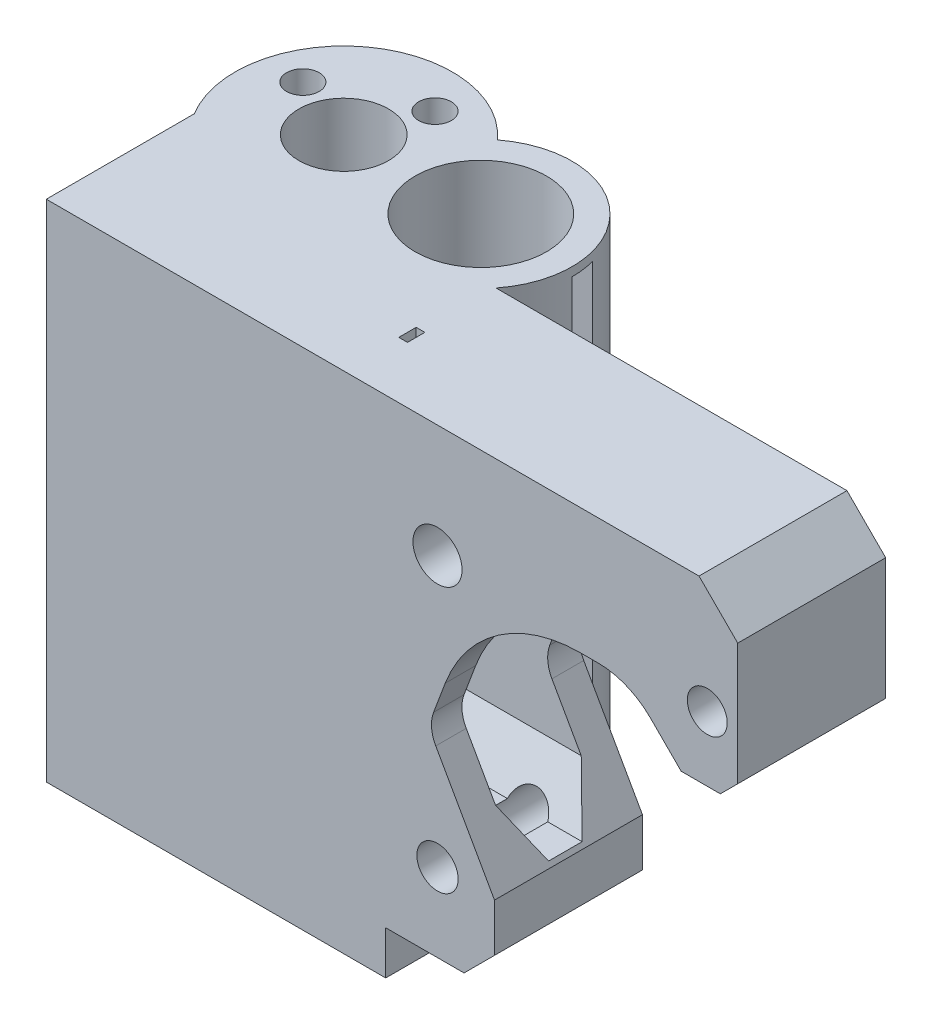
SolidWorks part; units mm, degrees
ref_plane "Front Plane" through (0, 0, 0) normal (0, 0, 1) x (1, 0, 0)
ref_plane "Top Plane" through (0, 0, 0) normal (0, 1, 0) x (1, 0, 0)
ref_plane "Right Plane" through (0, 0, 0) normal (1, 0, 0) x (0, 0, -1)
sketch "Sketch1" plane through (0, 0, 0) normal (0, 0, 1) x (1, 0, 0)
  line L0 (39, -53) -> (48, -53)
  line L1 (0, 0) -> (39, 0)
  line L2 (0, 0) -> (0, -58)
  line L3 (0, -58) -> (39, -58)
  line L4 (39, -53) -> (39, -58)
  line L5 (39, 0) -> (75, 0)
  line L6 (75, 0) -> (79.45, -4.45)
  line L7 (79.45, -4.45) -> (79.45, -18.45)
  line L8 (79.45, -18.45) -> (77.45, -20.45)
  line L9 (77.45, -20.45) -> (72.95, -20.45)
  line L10 (72.95, -20.45) -> (69.45, -16.95)
  line L12 (45.8405, -25.2376) -> (44.5009, -28.8048)
  line L13 (44.75, -32.0294) -> (51.5, -44)
  line L14 (51.5, -44) -> (51.5, -49.5)
  line L15 (61.4145, -14.45) -> (63.4145, -14.45)
  line L16 (51.5, -49.5) -> (48, -53)
  arc A5 (63.4145, -14.45) -> (69.45, -16.95) centre (63.4145, -22.9855) cw
  arc A6 (61.4145, -14.45) -> (45.8405, -25.2376) centre (61.4145, -31.0859) ccw
  arc A7 (44.5009, -28.8048) -> (44.75, -32.0294) centre (48.083, -30.15) ccw
  dimension "D1" = 58
  dimension "D2" = 39
  dimension "D3" = 75
  dimension "D4" = 4.45
  dimension "D5" = 135
  dimension "D6" = 14
  dimension "D7" = 2
  dimension "D8" = 3.5
  dimension "D9" = 6
  dimension "D10" = 5
  dimension "D11" = 4.5
  dimension "D12" = 130
  dimension "D13" = 3.5
  dimension "D14" = 5.5
  dimension "D15" = 6.75
  dimension "D16" = 9
  dimension "D17" = 13.85
  dimension "D18" = 3.417
  dimension "D19" = 2
extrude "Boss-Extrude1" add sketch "Sketch1" along normal blind 17
sketch "Sketch2" plane through (0, 0, 0) normal (0, 1, 0) x (1, 0, 0)
  line L0 (0, -17) -> (0, 6.5) construction
  line L1 (0, 6.5) -> (26.427, 6.5) construction
  circle A0 centre (26.427, 6.5) radius 10.5
  dimension "D2" = 21
  dimension "D1" = 23.5
  dimension "D3" = 26.427
extrude "Boss-Extrude2" add sketch "Sketch2" against normal up to surface (58 mm away) up to face at (19.5, -58, 8.5)
sketch "Sketch3" plane through (0, 0, 0) normal (0, 1, 0) x (1, 0, 0)
  line L0 (0, -17) -> (0, 20.4292) construction
  line L1 (10.6771, 6.5) -> (0, 6.5) construction
  line L2 (75, -17) -> (0, -17) construction
  circle A0 centre (10.6771, 6.5) radius 12.5
  dimension "D3" = 25
  dimension "D2" = 23.5
extrude "Boss-Extrude3" add sketch "Sketch3" against normal blind 13.5
sketch "Sketch4" plane through (0, 0, 0) normal (0, 1, 0) x (1, 0, 0)
  circle A0 centre (26.427, 6.5) radius 7.55
  circle A1 centre (10.6771, 6.5) radius 5.15
  dimension "D1" = 10.3
  dimension "D2" = 15.1
extrude "Cut-Extrude1" cut sketch "Sketch4" against normal through all
sketch "Sketch5" plane through (0, 0, 0) normal (-1, 0, 0) x (0, 0, 1)
  line L0 (10.5, -43.5) -> (6.65, -43.5)
  line L1 (6.65, -43.5) -> (3.65, -38)
  line L2 (3.65, -38) -> (3.65, -19)
  line L3 (3.65, -19) -> (6.65, -13.5)
  line L4 (6.65, -13.5) -> (10.5, -13.5)
  line L5 (10.5, -13.5) -> (13.5, -19)
  line L6 (13.5, -19) -> (13.5, -38)
  line L7 (13.5, -38) -> (10.5, -43.5)
  line L8 (17, 0) -> (0, 0) construction
  line L9 (17, 0) -> (17, -58) construction
  line L10 (8.5, -6) -> (8.5, -51) construction
  line L11 (8.5, -28.5) -> (38.7948, -28.5) construction
  line L12 (3.65, -38) -> (13.5, -38) construction
  line L13 (3.65, -19) -> (13.5, -19) construction
  circle A0 centre (8.5, -6) radius 4.05
  circle A1 centre (8.5, -51) radius 4.05
  dimension "D8" = 8.1
  dimension "D9" = 8.1
  dimension "D1" = 19
  dimension "D2" = 3
  dimension "D3" = 3.85
  dimension "D4" = 15
  dimension "D5" = 6
  dimension "D6" = 45
  dimension "D7" = 5.5
  dimension "D10" = 5.5
  dimension "D12" = 19
  dimension "D13" = 3.85
  dimension "D14" = 3
  dimension "D15" = 3
  dimension "D16" = 3.5
  dimension "D17" = 8.5
  dimension "D18" = 8.5
extrude "Cut-Extrude2" cut sketch "Sketch5" against normal blind 35
sketch "Sketch6" plane through (0, 0, 0) normal (0, 0, -1) x (-1, 0, 0)
  line L0 (-75.9503, -13) -> (-44.9503, -13) construction
  line L1 (-44.9503, -13) -> (-44.9503, -44) construction
  line L2 (-44.9503, -44) -> (-75.9503, -44) construction
  line L3 (-75.9503, -44) -> (-75.9503, -13) construction
  line L4 (-75.9503, -28.5) -> (-44.9503, -28.5) construction
  line L5 (-60.4503, -13) -> (-60.4503, -44) construction
  line L6 (-53.4306, -6) -> (-40.9864, -6) construction
  line L7 (-75, 0) -> (-34.6732, 0) construction
  line L8 (-60.4503, -51) -> (-40.9864, -51) construction
  line L9 (-40.9864, -6) -> (-40.9864, -51) construction
  line L10 (-40.9864, -28.5) -> (-48.7037, -28.5) construction
  circle A0 centre (-75.9503, -13) radius 2.2933
  circle A1 centre (-44.9503, -13) radius 2.8225
  circle A2 centre (-44.9503, -44) radius 2.3733
  circle A3 centre (-60.4503, -28.5) radius 11 construction
  point P14 (-60.4503, -28.5)
  dimension "D3" = 22
  dimension "D1" = 31
  dimension "D2" = 31
  dimension "D4" = 6
  dimension "D5" = 45
extrude "Cut-Extrude3" cut sketch "Sketch6" against normal through all
sketch "Sketch8" plane through (35, 0, 0) normal (-1, 0, 0) x (0, 0, 1)
  line L8 (10.5, -43.5) -> (13.5, -38)
  line L9 (13.5, -38) -> (13.5, -19)
  line L10 (13.5, -19) -> (10.5, -13.5)
  line L11 (10.5, -13.5) -> (6.65, -13.5)
  line L12 (6.65, -13.5) -> (3.65, -19)
  line L13 (3.65, -19) -> (3.65, -38)
  line L14 (3.65, -38) -> (6.65, -43.5)
  line L15 (6.65, -43.5) -> (10.5, -43.5)
  line L16 (10.5, -43.5) -> (13.5, -38)
  line L17 (13.5, -38) -> (13.5, -19)
  line L18 (13.5, -19) -> (10.5, -13.5)
  line L19 (10.5, -13.5) -> (6.65, -13.5)
  line L20 (6.65, -13.5) -> (3.65, -19)
  line L21 (3.65, -19) -> (3.65, -38)
  line L22 (3.65, -38) -> (6.65, -43.5)
  line L23 (6.65, -43.5) -> (10.5, -43.5)
  dimension "D1" = 0
extrude "Cut-Extrude4" cut sketch "Sketch8" against normal blind 20
sketch "Sketch10" plane through (0, 0, 0) normal (0, 1, 0) x (1, 0, 0)
  line L0 (13.5702, 14.0925) -> (10.6771, 6.5) construction
  line L1 (10.6771, 6.5) -> (3.0846, 9.3931) construction
  circle A0 centre (13.5702, 14.0925) radius 1.875
  circle A1 centre (3.0846, 9.3931) radius 1.875
  dimension "D3" = 3.75
  dimension "D4" = 3.75
  dimension "D1" = 90
  dimension "D2" = 8.125
  dimension "D5" = 8.125
extrude "Cut-Extrude6" cut sketch "Sketch10" against normal through all
sketch "Sketch11" plane through (0, -58, 0) normal (0, -1, 0) x (1, 0, 0)
  line L0 (0, 17) -> (0, 0) construction
  line L1 (35, 8.5) -> (34, 8.5)
  line L2 (35, 8.5) -> (35, 10.5)
  line L3 (35, 10.5) -> (34, 10.5)
  line L4 (34, 8.5) -> (34, 10.5)
  line L5 (0, 17) -> (39, 17) construction
  dimension "D1" = 35
  dimension "D2" = 1
  dimension "D3" = 2
  dimension "D4" = 6.5
extrude "Cut-Extrude7" cut sketch "Sketch11" against normal blind 8
ref_plane "Plane1" through (0, -29, 0) normal (0, 1, 0) x (1, 0, 0)
mirror "Mirror1" about plane through (0, -29, 0) normal (0, 1, 0) of "Cut-Extrude7"
sketch "Sketch13" plane through (0, -58, 0) normal (0, -1, 0) x (1, 0, 0)
  line L0 (26.427, -6.5) -> (36.5692, -9.2176) construction
  line L1 (26.427, -6.5) -> (9.2701, -6.5) construction
  line L2 (26.427, -6.5) -> (36.927, -6.5) construction
  line L3 (33.7197, -8.4541) -> (36.5692, -9.2176)
  line L4 (36.927, -6.5) -> (33.977, -6.5)
  arc A0 (33.7197, -8.4541) -> (33.977, -6.5) centre (26.427, -6.5) ccw
  arc A1 (15.927, -6.5) -> (36.927, -6.5) centre (26.427, -6.5) ccw construction
  arc A2 (18.1808, 0) -> (34.6732, 0) centre (26.427, -6.5) ccw construction
  circle A3 centre (26.427, -6.5) radius 7.55 construction
  dimension "D1" = 15
  dimension "D2" = 180
extrude "Cut-Extrude9" cut sketch "Sketch13" against normal blind 57 and the other way through all
